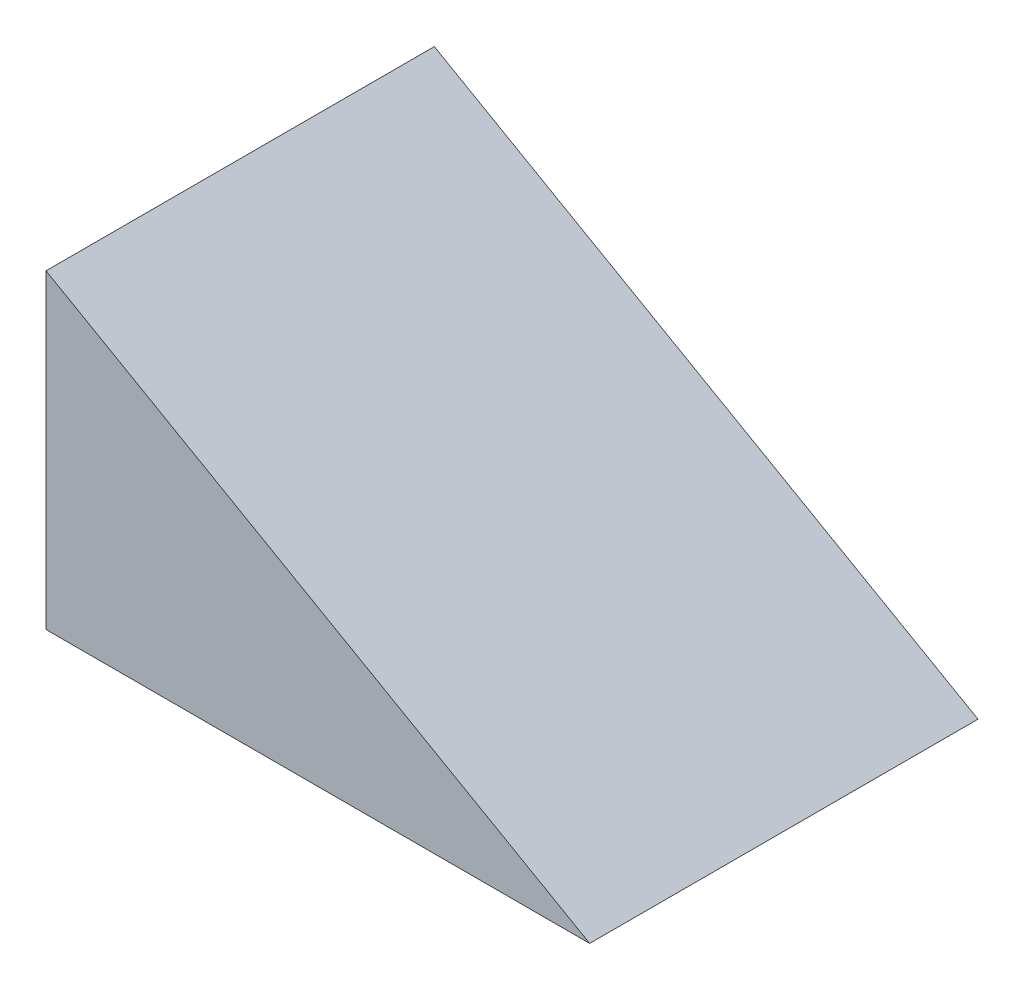
SolidWorks part; units mm, degrees
ref_plane "Front Plane" through (0, 0, 0) normal (0, 0, 1) x (1, 0, 0)
ref_plane "Top Plane" through (0, 0, 0) normal (0, 1, 0) x (1, 0, 0)
ref_plane "Right Plane" through (0, 0, 0) normal (1, 0, 0) x (0, 0, -1)
sketch "Sketch1" plane through (0, 0, 0) normal (0, 0, 1) x (1, 0, 0)
  line L0 (0, 0) -> (70, 0)
  line L1 (70, 0) -> (0, 40)
  line L2 (0, 40) -> (0, 0)
  dimension "D1" = 40
  dimension "D2" = 70
extrude "Boss-Extrude2" add sketch "Sketch1" along normal blind 50
